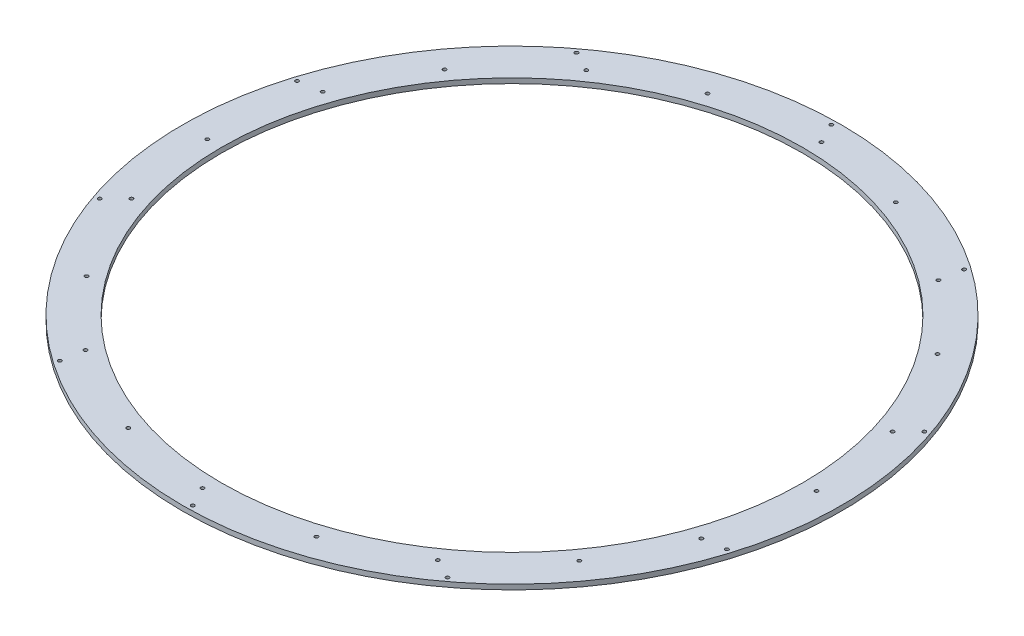
SolidWorks part; units mm, degrees
ref_plane "Front Plane" through (0, 0, 0) normal (0, 0, 1) x (1, 0, 0)
ref_plane "Top Plane" through (0, 0, 0) normal (0, 1, 0) x (1, 0, 0)
ref_plane "Right Plane" through (0, 0, 0) normal (1, 0, 0) x (0, 0, -1)
sketch "Sketch1" plane through (0, 0, 0) normal (0, 1, 0) x (1, 0, 0)
  circle A0 centre (0, 0) radius 291
  circle A1 centre (0, 0) radius 330
  dimension "D1" = 660
  dimension "D2" = 582
extrude "Boss-Extrude1" add sketch "Sketch1" against normal blind 5
sketch "Sketch2" plane through (0, 0, 0) normal (0, 1, 0) x (1, 0, 0)
  circle A5 centre (5.2385, -324.9578) radius 1.75
  circle A6 centre (94.2502, -290.0722) radius 1.75
  circle A7 centre (175.274, -249.6078) radius 1.75
  dimension "D1" = 3.5
extrude "Cut-Extrude1" cut sketch "Sketch2" against normal through all
pattern_circular "CirPattern1" count 10 over 360 about axis through (0, 0, 0) along (0, 1, 0) of "Cut-Extrude1"
